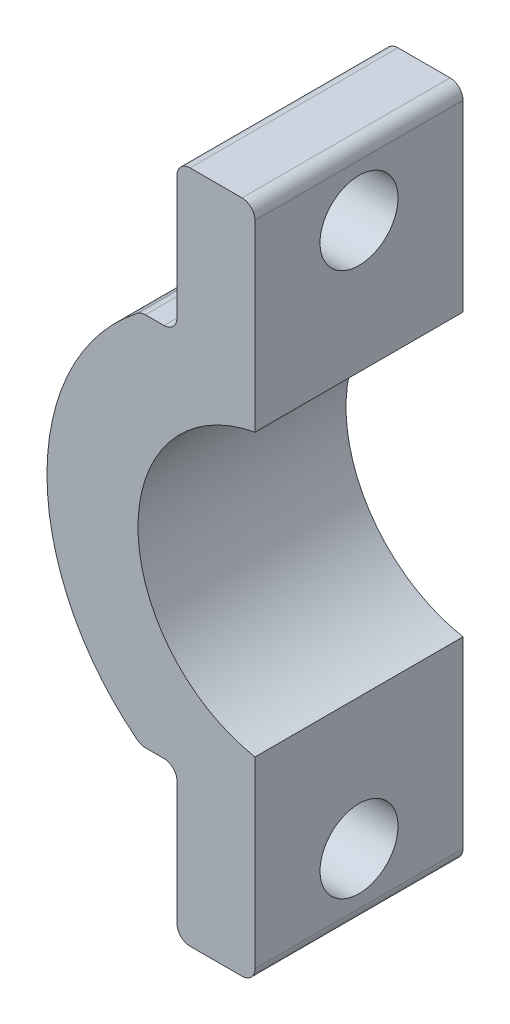
SolidWorks part; units mm, degrees
ref_plane "Plan de face" through (0, 0, 0) normal (0, 0, 1) x (1, 0, 0)
ref_plane "Plan de dessus" through (0, 0, 0) normal (0, 1, 0) x (1, 0, 0)
ref_plane "Plan de droite" through (0, 0, 0) normal (1, 0, 0) x (0, 0, -1)
sketch "Esquisse1" plane through (0, 0, 0) normal (0, 0, 1) x (1, 0, 0)
  circle A0 centre (0, 0) radius 13
  circle A1 centre (0, 0) radius 5.5
  dimension "D1" = 11
  dimension "D2" = 26
extrude "Boss.-Extru.1" add sketch "Esquisse1" along normal blind 8
sketch "Esquisse2" plane through (0, 0, 8) normal (0, 0, 1) x (1, 0, 0)
  line L1 (-1, 24.2432) -> (31.31, 24.2432)
  line L2 (-1, 24.2432) -> (-1, -25.575)
  line L3 (-1, -25.575) -> (31.31, -25.575)
  line L4 (31.31, 24.2432) -> (31.31, -25.575)
  dimension "D1" = 1
extrude "Enlèv. mat.-Extru.1" cut sketch "Esquisse2" against normal blind 8
sketch "Esquisse3" plane through (-1, 0, 0) normal (1, 0, 0) x (0, 0, -1)
  line L0 (-8, 12.9615) -> (-8, 5.4083) construction
  line L1 (-8, 12.9615) -> (0, 12.9615) construction
  line L2 (0, -12.9615) -> (-8, -12.9615) construction
  line L4 (-8, -5.4083) -> (-8, -12.9615) construction
  circle A0 centre (-4, 10.4615) radius 1.5
  circle A1 centre (-4, -10.4615) radius 1.5
  dimension "D1" = 3
  dimension "D4" = 3
  dimension "D2" = 4
  dimension "D3" = 2.5
  dimension "D5" = 2.5
  dimension "D6" = 4
extrude "Enlèv. mat.-Extru.2" cut sketch "Esquisse3" against normal blind 8
sketch "Esquisse4" plane through (0, 0, 8) normal (0, 0, 1) x (1, 0, 0)
  line L0 (-9, 8.9615) -> (-1, 8.9615) construction
  line L1 (-28.8712, 21.0445) -> (-4, 21.0445)
  line L2 (-28.8712, 21.0445) -> (-28.8712, 7.2115)
  line L3 (-28.8712, 7.2115) -> (-4, 7.2115)
  line L4 (-4, 21.0445) -> (-4, 7.2115)
  line L5 (-1, 12.9615) -> (-1, 5.4083) construction
  line L6 (-1, -5.4083) -> (-1, -12.9615) construction
  line L7 (-4, -7.2115) -> (-27.4321, -7.2115)
  line L8 (-4, -7.2115) -> (-4, -17.5209)
  line L9 (-4, -17.5209) -> (-27.4321, -17.5209)
  line L10 (-27.4321, -7.2115) -> (-27.4321, -17.5209)
  line L11 (-1, -8.9615) -> (-9, -8.9615) construction
  dimension "D1" = 1.75
  dimension "D2" = 3
  dimension "D3" = 3
  dimension "D4" = 1.75
extrude "Enlèv. mat.-Extru.3" cut sketch "Esquisse4" against normal blind 8
sketch "Esquisse6" plane through (0, 0, 8) normal (0, 0, 1) x (1, 0, 0)
  line L0 (-14.6892, -10.0493) -> (-4.8187, -7.6013)
  line L1 (-11.1335, 10.8925) -> (-4.4941, 7.7977)
  arc A0 (-4.4941, 7.7977) -> (-4.8187, -7.6013) centre (0, 0) ccw
  arc A1 (-11.1335, 10.8925) -> (-14.6892, -10.0493) centre (-3.9187, -1.1053) ccw
  point P7 (-5.2167, 7.3339)
  point P8 (-4.8187, -7.6013)
  point P9 (-4.4941, 7.7977)
  dimension "D1" = 9
  dimension "D2" = 14
extrude "Enlèv. mat.-Extru.4" cut sketch "Esquisse6" against normal blind 8
sketch "Esquisse7" plane through (0, 0, 0) normal (0, 0, -1) x (-1, 0, 0)
  line L1 (4, 7.2115) -> (1, 7.2115)
  line L2 (4, 7.2115) -> (4, 12.9615)
  line L3 (4, 12.9615) -> (1, 12.9615)
  line L4 (1, 7.2115) -> (1, 12.9615)
  line L5 (4, -7.2115) -> (1, -7.2115)
  line L6 (4, -7.2115) -> (4, -12.9615)
  line L7 (4, -12.9615) -> (1, -12.9615)
  line L8 (1, -7.2115) -> (1, -12.9615)
extrude "Boss.-Extru.3" add sketch "Esquisse7" against normal blind 8
sketch "Esquisse11" plane through (-1, 0, 0) normal (1, 0, 0) x (0, 0, -1)
  line L0 (-8, 12.9615) -> (-8, 5.4083) construction
  line L1 (-8, -5.4083) -> (-8, -12.9615) construction
  line L2 (-8, 12.9615) -> (0, 12.9615) construction
  line L3 (0, -12.9615) -> (-8, -12.9615) construction
  circle A0 centre (-4, 10.4615) radius 1.5
  circle A1 centre (-4, -10.4615) radius 1.5
  dimension "D1" = 4
  dimension "D5" = 3
  dimension "D6" = 3
  dimension "D2" = 4
  dimension "D3" = 2.5
  dimension "D4" = 2.5
extrude "Enlèv. mat.-Extru.5" cut sketch "Esquisse11" against normal blind 8 contours A0
fillet "Congé5" radius 0.5 2 edges at (-4, -12.9615, 4) (-4, 12.9615, 4)
fillet "Congé6" radius 0.5 2 edges at (-4, -7.2115, 4) (-4, 7.2115, 4)
fillet "Congé7" radius 0.5 2 edges at (-1, -12.9615, 4) (-1, 12.9615, 4)
fillet "Congé8" radius 0.5 2 edges at (-5.3847, -7.2115, 4) (-5.3847, 7.2115, 4)
